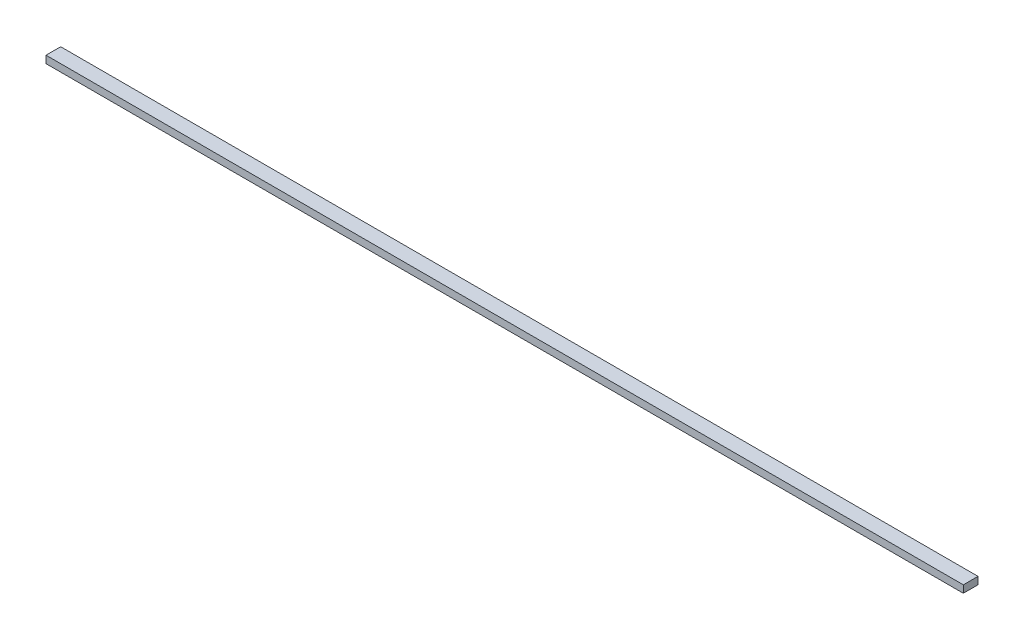
SolidWorks part; units mm, degrees
ref_plane "Front Plane" through (0, 0, 0) normal (0, 0, 1) x (1, 0, 0)
ref_plane "Top Plane" through (0, 0, 0) normal (0, 1, 0) x (1, 0, 0)
ref_plane "Right Plane" through (0, 0, 0) normal (1, 0, 0) x (0, 0, -1)
sketch "Sketch1" plane through (0, 0, 0) normal (0, 1, 0) x (1, 0, 0)
  line L0 (-625, 10) -> (625, -10) construction
  line L1 (-625, 10) -> (625, 10)
  line L2 (-625, 10) -> (-625, -10)
  line L3 (-625, -10) -> (625, -10)
  line L4 (625, 10) -> (625, -10)
  dimension "D1" = 1250
  dimension "D2" = 20
extrude "Boss-Extrude1" add sketch "Sketch1" along normal blind 10
